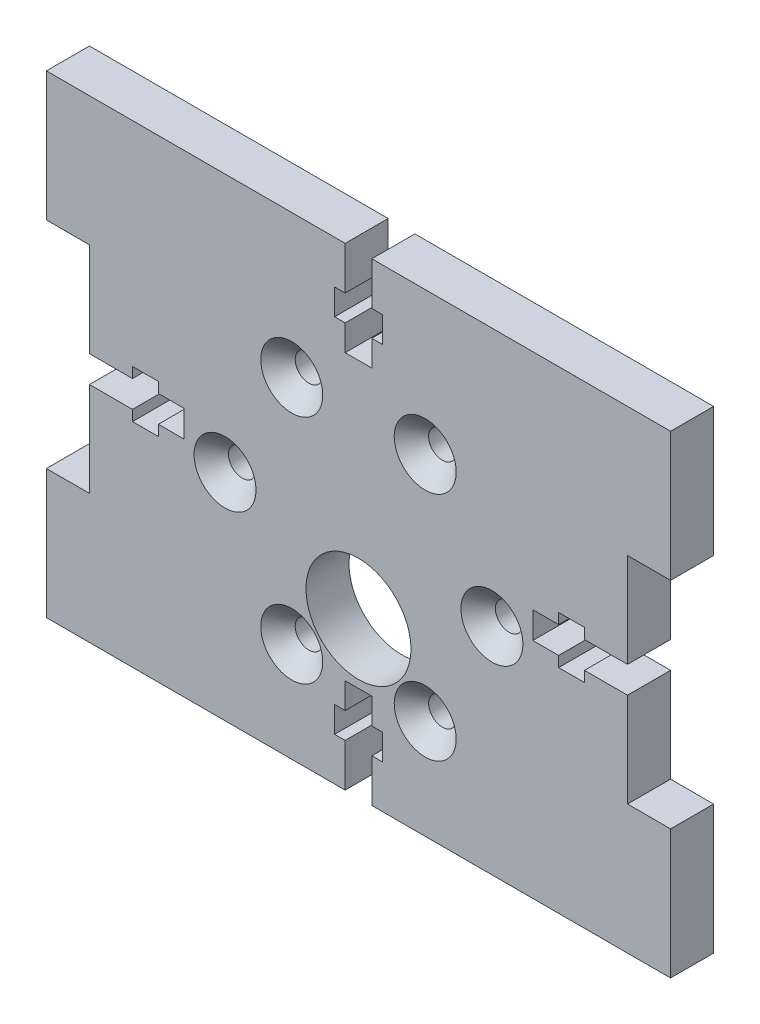
SolidWorks part; units mm, degrees
ref_plane "Plan de face" through (0, 0, 0) normal (0, 0, 1) x (1, 0, 0)
ref_plane "Plan de dessus" through (0, 0, 0) normal (0, 1, 0) x (1, 0, 0)
ref_plane "Plan de droite" through (0, 0, 0) normal (1, 0, 0) x (0, 0, -1)
ref_plane "Plan1" through (0, 0, 0) normal (0, 0, -1) x (-1, 0, 0)
sketch "Esquisse1" plane through (0, 0, 0) normal (0, 0, -1) x (-1, 0, 0)
  line L0 (-4.9964, 30) -> (-31.25, 30)
  line L1 (-31.25, 30) -> (-31.25, -25)
  line L2 (-31.25, -25) -> (-4.9964, -25)
  line L3 (-4.9964, -25) -> (-4.9964, 30)
extrude "Boss.-Extru.1" add sketch "Esquisse1" against normal blind 5
sketch "Esquisse2" plane through (31.25, 0, 0) normal (1, 0, 0) x (0, 0, -1)
  line L0 (0, 15) -> (-2.05, 15)
  line L1 (-2.05, 15) -> (-5, 17.95)
  line L2 (-5, 17.95) -> (-5, 30)
  line L3 (-5, 30) -> (0, 30)
  line L4 (0, 30) -> (0, 15)
extrude "Boss.-Extru.2" add sketch "Esquisse2" along normal blind 5
sketch "Esquisse3" plane through (31.25, 0, 0) normal (1, 0, 0) x (0, 0, -1)
  line L0 (-5, -12.95) -> (-2.05, -10)
  line L1 (-2.05, -10) -> (0, -10)
  line L2 (0, -10) -> (0, -25)
  line L3 (0, -25) -> (-5, -25)
  line L4 (-5, -25) -> (-5, -12.95)
extrude "Boss.-Extru.3" add sketch "Esquisse3" along normal blind 5
sketch "Esquisse4" plane through (0, 30, 0) normal (0, 1, 0) x (-1, 0, 0)
  line L0 (-4.9964, 5) -> (-7.9464, 5)
  line L1 (-7.9464, 5) -> (-4.9964, 2.05)
  line L2 (-4.9964, 2.05) -> (-4.9964, 5)
extrude "Enlèv. mat.-Extru.1" cut sketch "Esquisse4" against normal blind 5
sketch "Esquisse5" plane through (4.9964, 0, 0) normal (-1, 0, 0) x (0, 0, 1)
  line L0 (0, -25) -> (0, 25)
  line L1 (0, 25) -> (5, 25)
  line L2 (5, 25) -> (5, -25)
  line L3 (5, -25) -> (0, -25)
extrude "Boss.-Extru.4" add sketch "Esquisse5" along normal blind 36.2464
sketch "Esquisse6" plane through (-31.25, 0, 0) normal (-1, 0, 0) x (0, 0, 1)
  line L0 (0, -25) -> (0, -10)
  line L1 (0, -10) -> (2.05, -10)
  line L2 (2.05, -10) -> (5, -12.95)
  line L3 (5, -12.95) -> (5, -25)
  line L4 (5, -25) -> (0, -25)
extrude "Boss.-Extru.5" add sketch "Esquisse6" along normal blind 5
sketch "Esquisse7" plane through (-31.25, 0, 0) normal (-1, 0, 0) x (0, 0, 1)
  line L0 (0, 25) -> (5, 25)
  line L1 (5, 25) -> (5, 17.95)
  line L2 (5, 17.95) -> (2.05, 15)
  line L3 (2.05, 15) -> (0, 15)
  line L4 (0, 15) -> (0, 25)
extrude "Boss.-Extru.6" add sketch "Esquisse7" along normal blind 5
sketch "Esquisse8" plane through (0, 25, 0) normal (0, 1, 0) x (-1, 0, 0)
  line L0 (5.0006, 2.0542) -> (7.9464, 5)
  line L1 (7.9464, 5) -> (36.25, 5)
  line L2 (36.25, 5) -> (36.25, 0)
  line L3 (36.25, 0) -> (5.0006, 0)
  line L4 (5.0006, 0) -> (5.0006, 2.0542)
extrude "Boss.-Extru.7" add sketch "Esquisse8" along normal blind 5
hole_wizard "Diamètre du perçage Ø12.2 (12.2)1" positions "Esquisse10" profile "Esquisse9" hole size "Ø12.2" standard "Ansi Metric"
sketch "Esquisse10" plane through (0, 0, 5) normal (0, 0, 1) x (1, 0, 0)
  point P0 (0, -7)
sketch "Esquisse9" plane through (0, -7, 5) normal (1, 0, 0) x (0, -1, 0)
  line L0 (0, 0) -> (0, 5)
  line L1 (0, 5) -> (6.1, 5)
  line L2 (6.1, 5) -> (6.1, 0)
  line L5 (6.1, 0) -> (0, 0)
  line L11 (0, -6.35) -> (0, 107.95) construction
  dimension "Diamètre du perçage jusqu'au prochain" = 12.2
  dimension "Profondeur du perçage jusqu'au prochain" = 5
hole_wizard "Diamètre du perçage Ø3.2 (3.2)1" positions "Esquisse12" profile "Esquisse11" hole size "Ø3.2" standard "Ansi Metric" end condition through all
sketch "Esquisse12" plane through (0, 0, 5) normal (0, 0, 1) x (1, 0, 0)
  point P0 (-7.75, -13.4234)
  point P1 (15.5, 0)
  point P2 (-7.75, 13.4234)
  point P3 (7.75, 13.4234)
  point P4 (7.75, -13.4234)
  point P5 (-15.5, 0)
sketch "Esquisse11" plane through (-7.75, -13.4234, 5) normal (1, 0, 0) x (0, -1, 0)
  line L0 (0, 0) -> (0, 5)
  line L1 (0, 5) -> (1.6, 5)
  line L2 (1.6, 5) -> (1.6, 0)
  line L5 (1.6, 0) -> (0, 0)
  line L11 (0, -6.35) -> (0, 107.95) construction
  dimension "Diamètre du perçage jusqu'au prochain" = 3.2
  dimension "Profondeur du perçage jusqu'au prochain" = 5
fillet "Congé1" radius 1.6 6 edges at (4.9964, 27.5, 2.05) (33.75, -10, 2.05) (33.75, 15, 2.05) (-33.75, -10, 2.05) (-5.0006, 27.5, 2.0542) (-33.75, 15, 2.05)
sketch "Esquisse13" plane through (0, 0, 5) normal (0, 0, 1) x (1, 0, 0)
  line L1 (-36.25, 17.95) -> (-31.25, 17.95)
  line L2 (-36.25, 17.95) -> (-36.25, 15)
  line L3 (-36.25, 15) -> (-31.25, 15)
  line L4 (-31.25, 17.95) -> (-31.25, 15)
  line L5 (-36.25, -10) -> (-31.25, -10)
  line L6 (-36.25, -10) -> (-36.25, -12.95)
  line L7 (-36.25, -12.95) -> (-31.25, -12.95)
  line L8 (-31.25, -10) -> (-31.25, -12.95)
  line L9 (-7.9464, 30) -> (-5.0006, 30)
  line L10 (-7.9464, 30) -> (-7.9464, 25)
  line L11 (-7.9464, 25) -> (-5.0006, 25)
  line L12 (-5.0006, 30) -> (-5.0006, 25)
  line L13 (4.9964, 30) -> (7.9464, 30)
  line L14 (4.9964, 30) -> (4.9964, 25)
  line L15 (4.9964, 25) -> (7.9464, 25)
  line L16 (7.9464, 30) -> (7.9464, 25)
  line L17 (31.25, 17.95) -> (36.25, 17.95)
  line L18 (31.25, 17.95) -> (31.25, 15)
  line L19 (31.25, 15) -> (36.25, 15)
  line L20 (36.25, 17.95) -> (36.25, 15)
  line L21 (31.25, -10) -> (36.25, -10)
  line L22 (31.25, -10) -> (31.25, -12.95)
  line L23 (31.25, -12.95) -> (36.25, -12.95)
  line L24 (36.25, -10) -> (36.25, -12.95)
  line L25 (-5.0006, 30) -> (4.9964, 30)
  line L26 (-5.0006, 30) -> (-5.0006, 25)
  line L27 (-5.0006, 25) -> (4.9964, 25)
  line L28 (4.9964, 30) -> (4.9964, 25)
  line M9 (7.9464, 30) -> (7.9464, 25)
  line M10 (7.9464, 25) -> (-7.9464, 25)
  line M11 (-7.9464, 25) -> (-7.9464, 30)
  line M14 (-36.25, 17.95) -> (-31.25, 17.95)
  line M15 (-31.25, 17.95) -> (-31.25, -12.95)
  line M16 (-31.25, -12.95) -> (-36.25, -12.95)
  line M20 (36.25, -12.95) -> (31.25, -12.95)
  line M21 (31.25, -12.95) -> (31.25, 17.95)
  line M22 (31.25, 17.95) -> (36.25, 17.95)
extrude "Boss.-Extru.8" add sketch "Esquisse13" against normal blind 5 contours L25 L12 L14 M10 | L12 L9 M11 M10 | L13 L14 M10 M9 | L20 L19 M22 M21 | L24 L21 M21 M20 | L5 L6 M16 M15 | L2 L3 M15 M14
sketch "Esquisse14" plane through (0, 0, 5) normal (0, 0, 1) x (1, 0, 0)
  line L0 (1.55, 19) -> (-1.55, 19)
  line L1 (1.55, 19) -> (1.55, 30)
  line L2 (1.55, 30) -> (-1.55, 30)
  line L3 (-1.55, 19) -> (-1.55, 30)
  line L4 (2.78, 22) -> (-2.77, 22)
  line L5 (2.78, 22) -> (2.78, 25)
  line L6 (2.78, 25) -> (-2.77, 25)
  line L7 (-2.77, 22) -> (-2.77, 25)
  line L8 (-20.25, 0.95) -> (-31.25, 0.95)
  line L9 (-20.25, 0.95) -> (-20.25, 4.05)
  line L10 (-20.25, 4.05) -> (-31.25, 4.05)
  line L11 (-31.25, 0.95) -> (-31.25, 4.05)
  line L12 (-23.25, -0.28) -> (-26.25, -0.28)
  line L13 (-23.25, -0.28) -> (-23.25, 5.27)
  line L14 (-23.25, 5.27) -> (-26.25, 5.27)
  line L15 (-26.25, -0.28) -> (-26.25, 5.27)
  line L18 (-36.25, 30) -> (36.25, 30) construction
  line L19 (-31.25, -10) -> (-31.25, 15) construction
  line L20 (-31.25, -10) -> (-36.25, -10) construction
  line L21 (0, 0) -> (0, 11.8782) construction
  line L22 (26.25, -0.28) -> (26.25, 5.27)
  line L23 (23.25, 5.27) -> (26.25, 5.27)
  line L24 (23.25, -0.28) -> (23.25, 5.27)
  line L25 (23.25, -0.28) -> (26.25, -0.28)
  line L26 (31.25, 0.95) -> (31.25, 4.05)
  line L27 (20.25, 4.05) -> (31.25, 4.05)
  line L28 (20.25, 0.95) -> (20.25, 4.05)
  line L29 (20.25, 0.95) -> (31.25, 0.95)
  line L30 (36.25, 30) -> (36.25, 15) construction
  line L31 (20.25, 2.5) -> (-20.25, 2.5) construction
  line L32 (-2.77, -17) -> (-2.77, -20)
  line L33 (2.78, -20) -> (-2.77, -20)
  line L34 (2.78, -17) -> (2.78, -20)
  line L35 (2.78, -17) -> (-2.77, -17)
  line L36 (-1.55, -14) -> (-1.55, -25)
  line L37 (1.55, -25) -> (-1.55, -25)
  line L38 (1.55, -14) -> (1.55, -25)
  line L39 (1.55, -14) -> (-1.55, -14)
  dimension "D1" = 3
  dimension "D2" = 5
  dimension "D3" = 5.55
  dimension "D4" = 3.1
  dimension "D5" = 1.23
  dimension "D6" = 11
  dimension "D7" = 3
  dimension "D8" = 5
  dimension "D9" = 5.55
  dimension "D10" = 3.1
  dimension "D11" = 1.23
  dimension "D12" = 0
  dimension "D13" = 34.7
  dimension "D14" = 0
  dimension "D15" = 10.95
  dimension "D16" = 3
extrude "Enlèv. mat.-Extru.2" cut sketch "Esquisse14" against normal blind 5
chamfer "Chanfrein1" distance 2 angle 45 6 edges at (-13.9, 0, 5) (-6.15, -13.4234, 5) (9.35, -13.4234, 5) (17.1, 0, 5) (9.35, 13.4234, 5) (-6.15, 13.4234, 5)
